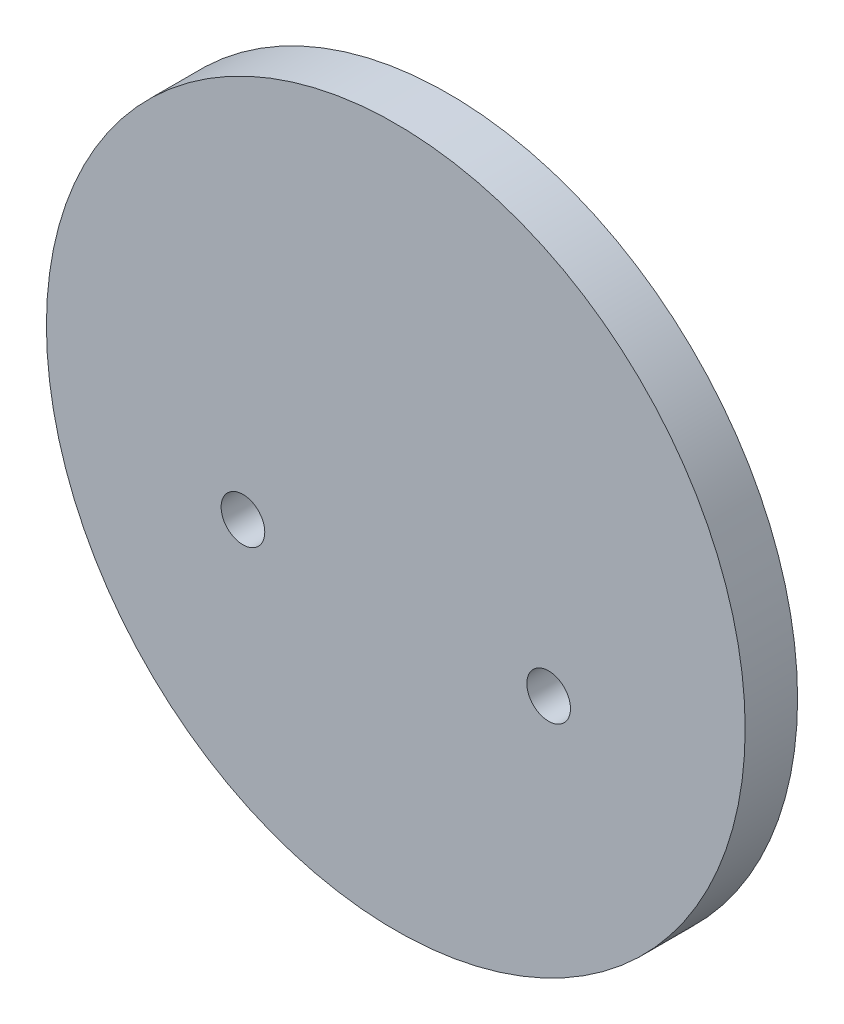
SolidWorks part; units mm, degrees
ref_plane "Front Plane" through (0, 0, 0) normal (0, 0, 1) x (1, 0, 0)
ref_plane "Top Plane" through (0, 0, 0) normal (0, 1, 0) x (1, 0, 0)
ref_plane "Right Plane" through (0, 0, 0) normal (1, 0, 0) x (0, 0, -1)
sketch "Sketch3" plane through (0, 0, 0) normal (0, 0, 1) x (1, 0, 0)
  circle A0 centre (0, 0) radius 40
extrude "Boss-Extrude1" add sketch "Sketch3" along normal blind 6
sketch "Sketch4" plane through (0, 0, 6) normal (0, 0, 1) x (1, 0, 0)
  line L0 (-41.6169, 0) -> (47.0034, 0) construction
  line L1 (0, -43.8292) -> (0, 42.6109) construction
  line L2 (0, 0) -> (0, -8)
  line L3 (0, -8) -> (-17.5, -8)
  line L4 (0, -8) -> (17.5, -8)
  circle A0 centre (-17.5, -8) radius 2.1
  circle A1 centre (17.5, -8) radius 2.1
  point P5 (0, 0)
extrude "Cut-Extrude1" cut sketch "Sketch4" against normal through all
ref_point "Point1"
ref_point "Point2"
sketch "Sketch5" plane through (0, 0, 0) normal (0, 0, -1) x (-1, 0, 0)
  circle A0 centre (-17.5, -8) radius 5
  circle A1 centre (17.5, -8) radius 5
extrude "Cut-Extrude2" cut sketch "Sketch5" against normal blind 1.5
other "Move Face1" face at (-15.4, -8, 6) face at (19.6, -8, 6) parameters "D1"=0.4
